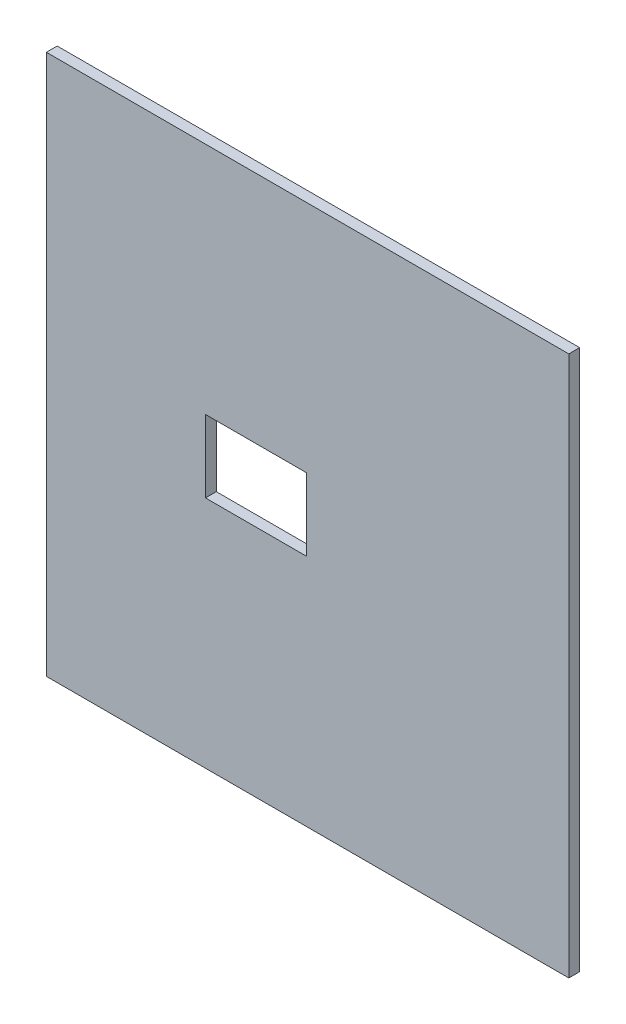
SolidWorks part; units mm, degrees
material "ABS"
ref_plane "Front Plane" through (0, 0, 0) normal (0, 0, 1) x (1, 0, 0)
ref_plane "Top Plane" through (0, 0, 0) normal (0, 1, 0) x (1, 0, 0)
ref_plane "Right Plane" through (0, 0, 0) normal (1, 0, 0) x (0, 0, -1)
sketch "Sketch1" plane through (0, 0, 0) normal (0, 0, 1) x (1, 0, 0)
  line L1 (-72.25, -74.75) -> (72.25, -74.75)
  line L2 (-72.25, -74.75) -> (-72.25, 74.75)
  line L3 (-72.25, 74.75) -> (72.25, 74.75)
  line L4 (72.25, -74.75) -> (72.25, 74.75)
  line L5 (-72.25, -74.75) -> (72.25, 74.75) construction
  line L6 (-72.25, 74.75) -> (72.25, -74.75) construction
  point P0 (0, 0)
  dimension "D1" = 144.5
  dimension "D2" = 149.5
extrude "Boss-Extrude1" add sketch "Sketch1" along normal blind 3
sketch "Sketch2" plane through (0, 0, 3) normal (0, 0, 1) x (1, 0, 0)
  line L0 (72.25, 0) -> (-72.25, 0) construction
  line L1 (72.25, -74.75) -> (72.25, 74.75) construction
  line L2 (-72.25, 74.75) -> (-72.25, -74.75) construction
  line L4 (-28.25, 10) -> (-0.25, 10)
  line L5 (-28.25, 10) -> (-28.25, -10)
  line L6 (-28.25, -10) -> (-0.25, -10)
  line L7 (-0.25, 10) -> (-0.25, -10)
  line L8 (-28.25, 10) -> (-0.25, -10) construction
  line L9 (-28.25, -10) -> (-0.25, 10) construction
  point P6 (-14.25, 0)
  dimension "D1" = 20
  dimension "D2" = 28
  dimension "D3" = 58
extrude "Cut-Extrude1" cut sketch "Sketch2" against normal up to next
